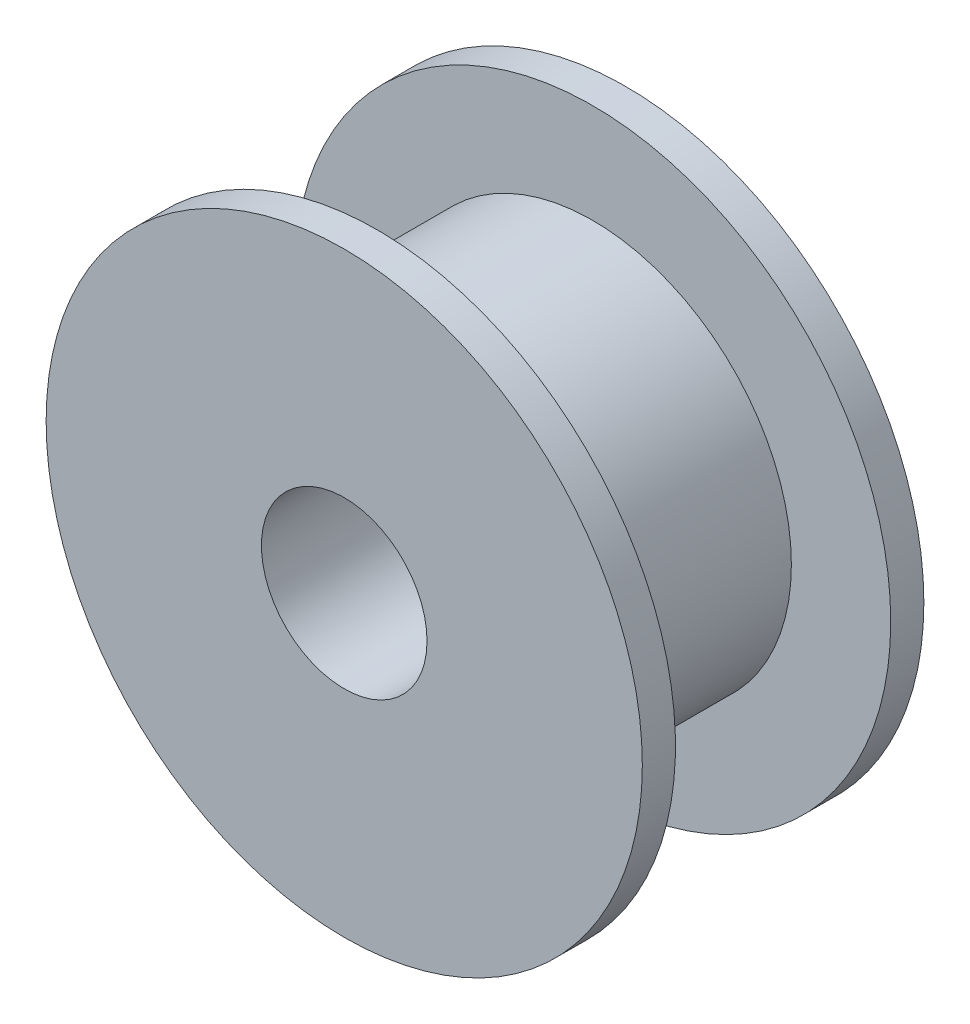
SolidWorks part; units mm, degrees
ref_plane "Front Plane" through (0, 0, 0) normal (0, 0, 1) x (1, 0, 0)
ref_plane "Top Plane" through (0, 0, 0) normal (0, 1, 0) x (1, 0, 0)
ref_plane "Right Plane" through (0, 0, 0) normal (1, 0, 0) x (0, 0, -1)
sketch "Sketch2" plane through (0, 0, 0) normal (0, 0, 1) x (1, 0, 0)
  circle A0 centre (0, 0) radius 9
  circle A1 centre (0, 0) radius 2.5
  dimension "D1" = 18
  dimension "D2" = 5
extrude "Boss-Extrude1" add sketch "Sketch2" along normal blind 8.5
sketch "Sketch4" plane through (0, 0, 0) normal (1, 0, 0) x (0, 0, -1)
  line L0 (-8.5, 0) -> (0, 0) construction
  line L2 (-8.5, 9) -> (-8.5, -9) construction
  line L4 (-7.5, 9.7821) -> (-7.5, 6)
  line L5 (-7.5, 6) -> (-1, 6)
  line L6 (-1, 6) -> (-1, 9.7821)
  line L7 (-1, 9.7821) -> (-7.5, 9.7821)
revolve "Cut-Revolve1" cut sketch "Sketch4" angle 360 about L0
